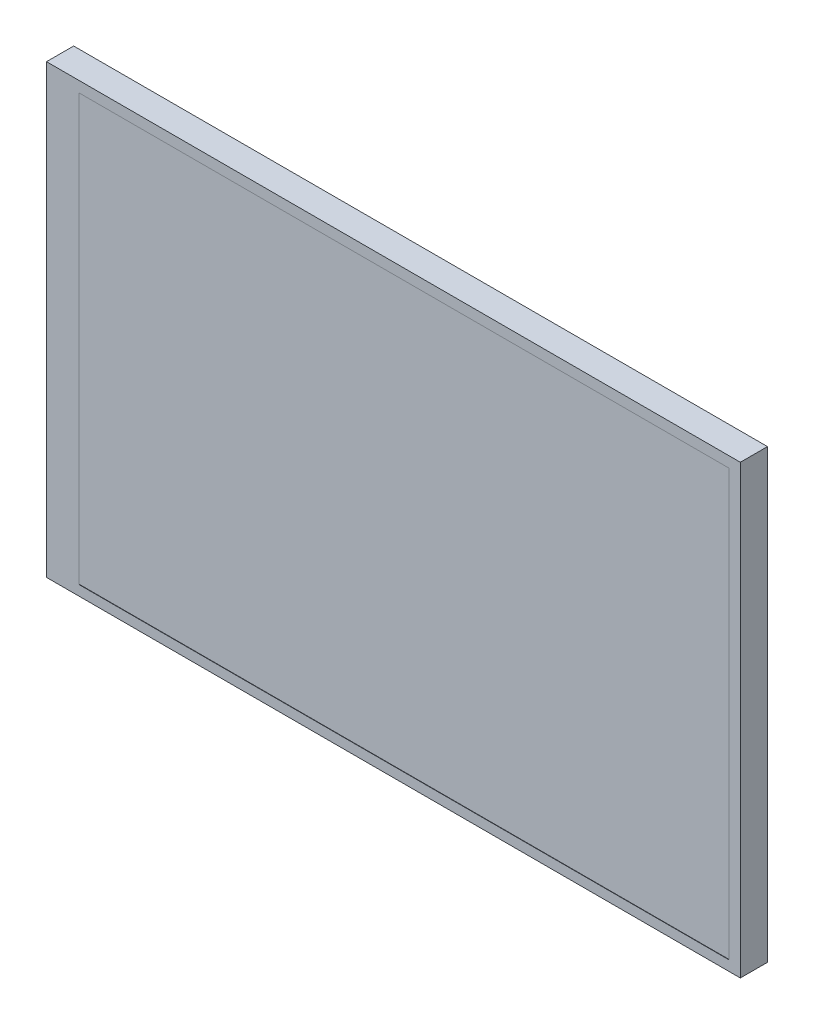
SolidWorks part; units mm, degrees
material "Plastique personnalisé"
ref_plane "Plan de face" through (0, 0, 0) normal (0, 0, 1) x (1, 0, 0)
ref_plane "Plan de dessus" through (0, 0, 0) normal (0, 1, 0) x (1, 0, 0)
ref_plane "Plan de droite" through (0, 0, 0) normal (1, 0, 0) x (0, 0, -1)
sketch "Esquisse1" plane through (0, 0, 0) normal (0, 0, 1) x (1, 0, 0)
  line L1 (0, 0) -> (94.57, 0)
  line L2 (0, 0) -> (0, 60.88)
  line L3 (0, 60.88) -> (94.57, 60.88)
  line L4 (94.57, 0) -> (94.57, 60.88)
  dimension "D1" = 94.57
  dimension "D2" = 60.88
extrude "Boss.-Extru.1" add sketch "Esquisse1" along normal blind 3.7
sketch "Esquisse2" plane through (0, 0, 3.7) normal (0, 0, 1) x (1, 0, 0)
  line L1 (93.0246, 59.4132) -> (4.3952, 59.4132)
  line L2 (93.0246, 59.4132) -> (93.0246, 1.3718)
  line L3 (93.0246, 1.3718) -> (4.3952, 1.3718)
  line L4 (4.3952, 59.4132) -> (4.3952, 1.3718)
extrude "Enlèv. mat.-Extru.1" cut sketch "Esquisse2" against normal blind 0.05
sketch "Esquisse3" plane through (0, 0, 0) normal (0, 0, -1) x (-1, 0, 0)
  line L0 (0, 60.88) -> (0, 0) construction
  line L1 (0, 30.44) -> (-11.0996, 30.44) construction
  line L2 (-94.57, 0) -> (-94.57, 60.88) construction
  line L3 (-11.0996, 30.44) -> (-40, 30.44) construction
  line L4 (-40, 30.44) -> (-35.9977, 30.44) construction
  line L5 (0, 40.94) -> (35.7726, 40.94) construction
  line L6 (0, 19.94) -> (35.7726, 19.94) construction
  line L7 (-9.0996, 9.4411) -> (0, 9.4411)
  line L8 (-13.0996, 40.94) -> (-40, 40.94)
  line L9 (0, 40.94) -> (0, 19.94)
  line L10 (-13.0996, 19.94) -> (-40, 19.94)
  line L11 (-40, 40.94) -> (-40, 19.94)
  line L12 (-11.0996, 30.44) -> (0, 30.44)
  line L13 (-11.0996, 11.4411) -> (-11.0996, 17.94)
  line L14 (-9.0996, 51.4389) -> (0, 51.4389)
  line L15 (0, 9.4411) -> (0, 51.4389)
  line L16 (-11.0996, 42.94) -> (-11.0996, 49.4389)
  line L17 (-40, 30.44) -> (-94.57, 30.44) construction
  line L19 (-35.9977, 20.6921) -> (-35.9977, 40.1879) construction
  line L21 (-35.9977, 40.1879) -> (-39.8851, 40.1879)
  line L22 (-35.9977, 40.1879) -> (-35.9977, 20.6921)
  line L23 (-35.9977, 20.6921) -> (-39.8851, 20.6921)
  line L24 (-39.8851, 40.1879) -> (-39.8851, 20.6921)
  arc A0 (-11.0996, 17.94) -> (-13.0996, 19.94) centre (-13.0996, 17.94) ccw
  arc A1 (-11.0996, 42.94) -> (-13.0996, 40.94) centre (-13.0996, 42.94) cw
  arc A2 (-9.0996, 9.4411) -> (-11.0996, 11.4411) centre (-9.0996, 11.4411) cw
  arc A3 (-11.0996, 49.4389) -> (-9.0996, 51.4389) centre (-9.0996, 49.4389) cw
  point P24 (-11.0996, 19.94)
  point P27 (-11.0996, 40.94)
  point P30 (-11.0996, 9.4411)
  point P33 (-11.0996, 51.4389)
  dimension "D4" = 2
  dimension "D1" = 10.5
  dimension "D2" = 10.5
  dimension "D3" = 40
extrude "Boss.-Extru.2" add sketch "Esquisse3" along normal blind 0.05
sketch "Esquisse4" plane through (0, 0, 0) normal (0, 0, -1) x (-1, 0, 0)
  line L1 (-35.9977, 20.6921) -> (-39.8851, 20.6921)
  line L2 (-35.9977, 20.6921) -> (-35.9977, 40.1879)
  line L3 (-35.9977, 40.1879) -> (-39.8851, 40.1879)
  line L4 (-39.8851, 20.6921) -> (-39.8851, 40.1879)
extrude "Boss.-Extru.3" add sketch "Esquisse4" along normal blind 0.1
